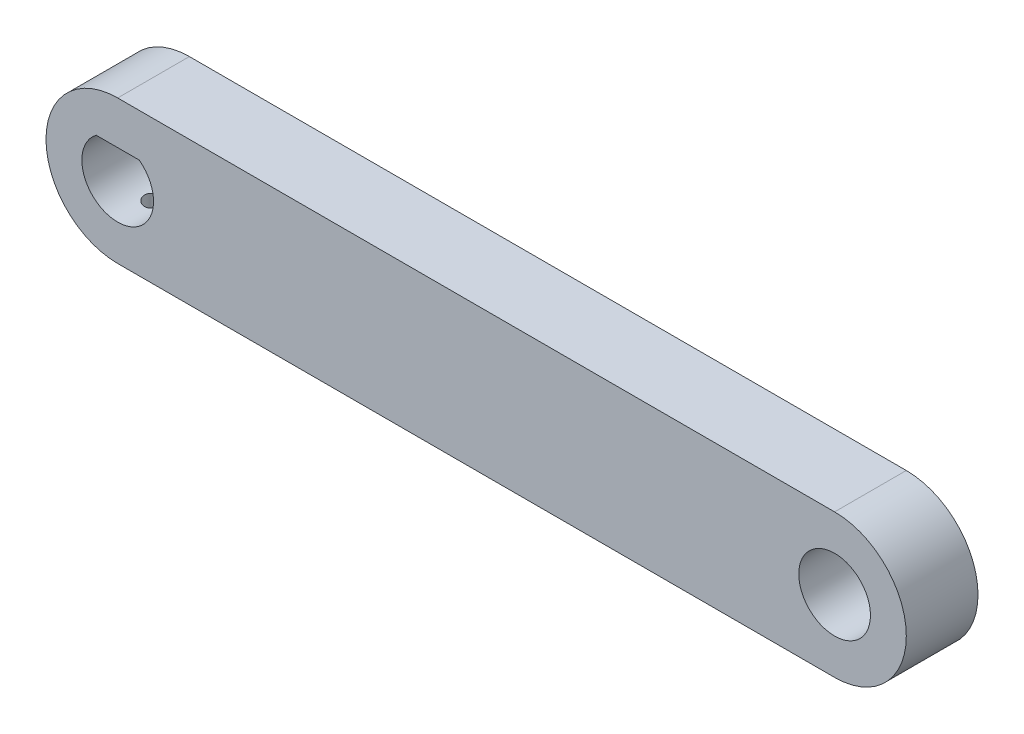
SolidWorks part; units mm, degrees
ref_plane "Front" through (0, 0, 0) normal (0, 0, 1) x (1, 0, 0)
ref_plane "Top" through (0, 0, 0) normal (0, 1, 0) x (1, 0, 0)
ref_plane "Right" through (0, 0, 0) normal (1, 0, 0) x (0, 0, -1)
sketch "草图1" plane through (0, 0, 0) normal (0, 0, 1) x (1, 0, 0)
  line L0 (-53, 4) -> (-47, 4)
  line L1 (-50, 10) -> (50, 10)
  line L3 (-50, -10) -> (50, -10)
  arc A0 (-50, 10) -> (-50, -10) centre (-50, 0) ccw
  arc A1 (50, 10) -> (50, -10) centre (50, 0) cw
  arc A2 (-53, 4) -> (-47, 4) centre (-50, 0) ccw
  circle A3 centre (50, 0) radius 5
  point P0 (0, 0)
  dimension "D3" = 10
  dimension "D4" = 10
  dimension "D1" = 100
  dimension "D2" = 20
extrude "凸台-拉伸1" add sketch "草图1" along normal blind 10
sketch "草图2" plane through (0, -10, 0) normal (0, -1, 0) x (1, 0, 0)
  line L0 (-50, 10) -> (-50, 0) construction
  circle A0 centre (-50, 5) radius 1.25
  dimension "D1" = 2.5
extrude "切除-拉伸1" cut sketch "草图2" against normal blind 10
